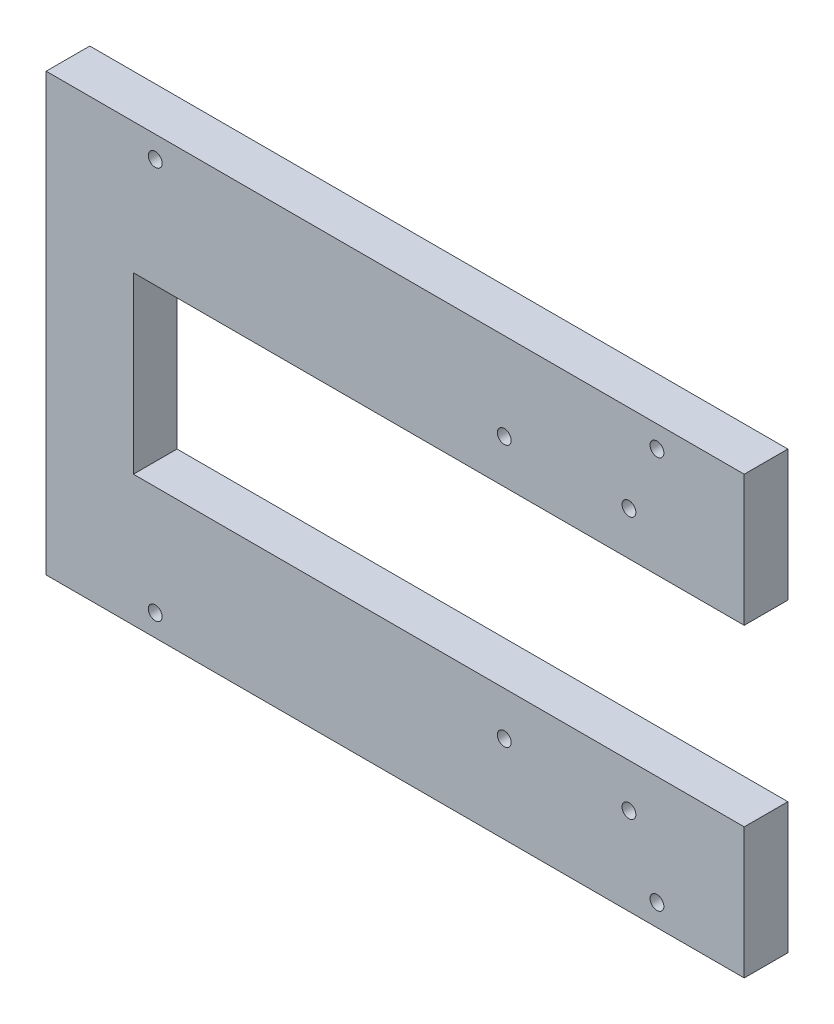
SolidWorks part; units mm, degrees
ref_plane "Front Plane" through (0, 0, 0) normal (0, 0, 1) x (1, 0, 0)
ref_plane "Top Plane" through (0, 0, 0) normal (0, 1, 0) x (1, 0, 0)
ref_plane "Right Plane" through (0, 0, 0) normal (1, 0, 0) x (0, 0, -1)
sketch "Sketch1" plane through (0, 0, 0) normal (0, 0, 1) x (1, 0, 0)
  line L0 (-53.5376, 64.885) -> (106.4624, 64.885)
  line L1 (-53.5376, -35.115) -> (106.4624, -35.115)
  line L2 (-53.5376, 64.885) -> (-53.5376, -35.115)
  line L3 (106.4624, 64.885) -> (106.4624, 34.885)
  line L4 (106.4624, -35.115) -> (106.4624, -5.115)
  line L5 (106.4624, -5.115) -> (-33.5376, -5.115)
  line L6 (106.4624, 34.885) -> (-33.5376, 34.885)
  line L7 (-33.5376, 34.885) -> (-33.5376, -5.115)
  circle A0 centre (51.4624, 44.885) radius 1.5875
  circle A1 centre (80.0374, 44.885) radius 1.5875
  circle A2 centre (51.4624, -15.115) radius 1.5875
  circle A3 centre (80.0374, -15.115) radius 1.5875
  circle A4 centre (-28.5376, 59.885) radius 1.5875
  circle A5 centre (86.4624, 59.885) radius 1.5875
  circle A6 centre (-28.5376, -30.115) radius 1.5875
  circle A7 centre (86.4624, -30.115) radius 1.5875
  dimension "D3" = 55
  dimension "D4" = 3.175
  dimension "D7" = 10
  dimension "D10" = 3.175
  dimension "D13" = 3.175
  dimension "D16" = 3.175
  dimension "D19" = 3.175
  dimension "D1" = 100
  dimension "D2" = 160
  dimension "D5" = 28.575
  dimension "D6" = 10
  dimension "D8" = 30
  dimension "D9" = 140
  dimension "D11" = 5
  dimension "D12" = 25
  dimension "D14" = 5
  dimension "D15" = 20
  dimension "D17" = 25
  dimension "D18" = 5
  dimension "D20" = 5
  dimension "D21" = 20
extrude "Boss-Extrude1" add sketch "Sketch1" along normal blind 10
